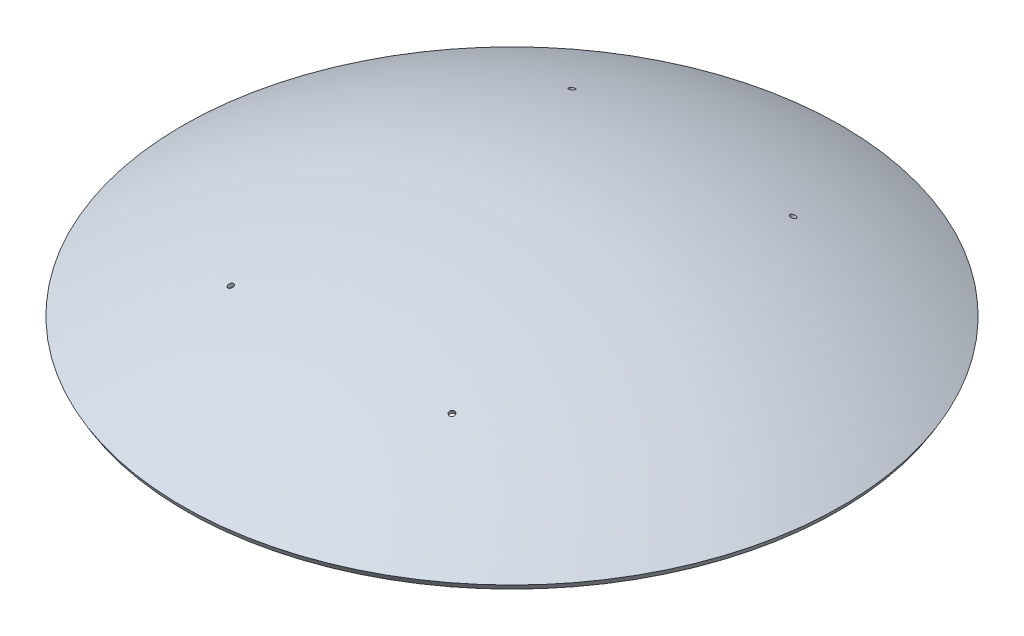
SolidWorks part; units mm, degrees
ref_plane "Front Plane" through (0, 0, 0) normal (0, 0, 1) x (1, 0, 0)
ref_plane "Top Plane" through (0, 0, 0) normal (0, 1, 0) x (1, 0, 0)
ref_plane "Right Plane" through (0, 0, 0) normal (1, 0, 0) x (0, 0, -1)
sketch "Sketch1" plane through (0, 0, 0) normal (0, 0, 1) x (1, 0, 0)
  line L0 (0, 0) -> (0, 274741.9116)
  line L1 (0, 0) -> (-146813.6761, 254288.7462)
  arc A0 (0, 237500) -> (-118750, 205681.0334) centre (0, 0) ccw
  arc A1 (0, 236250) -> (-118125, 204598.5016) centre (0, 0) ccw
  arc A2 (0, 235000) -> (-117500, 203515.9699) centre (0, 0) ccw
  dimension "D1" = 470000
  dimension "D2" = 472500
  dimension "D3" = 475000
  dimension "D4" = 30
revolve "Revolve1" add sketch "Sketch1" angle 360 about L0
sketch "Sketch2" plane through (0, 0, 0) normal (1, 0, 0) x (0, 0, -1)
  line L0 (0, 0) -> (102266.9265, 0)
ref_plane "Plane1" through (0, 0, 0) normal (0.9848, -0.1736, 0) x (0, 0, -1)
sketch "Sketch3" plane through (0, 0, 0) normal (0.9848, -0.1736, 0) x (0, 0, -1)
  line L0 (-54172.853, 202175.8398) -> (-66610.5059, 248593.7923)
  line L1 (-53239.6522, 202556.7904) -> (-65651.2224, 248877.4009)
  line L2 (-51373.2507, 203318.6916) -> (-63732.6554, 249444.6181)
  line L3 (-73457.2558, 246569.576) -> (-53221.9898, 252552.0575)
  line L4 (-66116.8943, 197300.051) -> (-43944.3479, 206351.3135)
  line L5 (2897.7775, 776.4571) -> (-67809.8472, 264660.9049) construction
  line L6 (965.9258, 258.819) -> (-69741.6989, 264143.2668) construction
  line L7 (0, 0) -> (-70707.6247, 263884.4478) construction
  line L8 (0, 0) -> (0, 275834.0255)
  arc A0 (-58566.8416, 230165.5384) -> (-61469.5232, 229407.3837) centre (0, 0) ccw
  arc A1 (-58243.2918, 228958.0343) -> (-61145.9994, 228199.9765) centre (0, 0) ccw
  arc A2 (-57919.7418, 227750.5291) -> (-60822.4756, 226992.5692) centre (0, 0) ccw
  dimension "D3" = 470000
  dimension "D4" = 472500
  dimension "D5" = 475000
  dimension "D6" = 15
  dimension "D1" = 1000
  dimension "D2" = 3000
revolve "Cut-Revolve1" cut sketch "Sketch3" angle 360 about L0
mirror "Mirror1" about plane through (0, 0, 0) normal (1, 0, 0) of "Cut-Revolve1"
mirror "Mirror2" about plane through (0, 0, 0) normal (0, 0, 1) of "Mirror1", "Cut-Revolve1"
